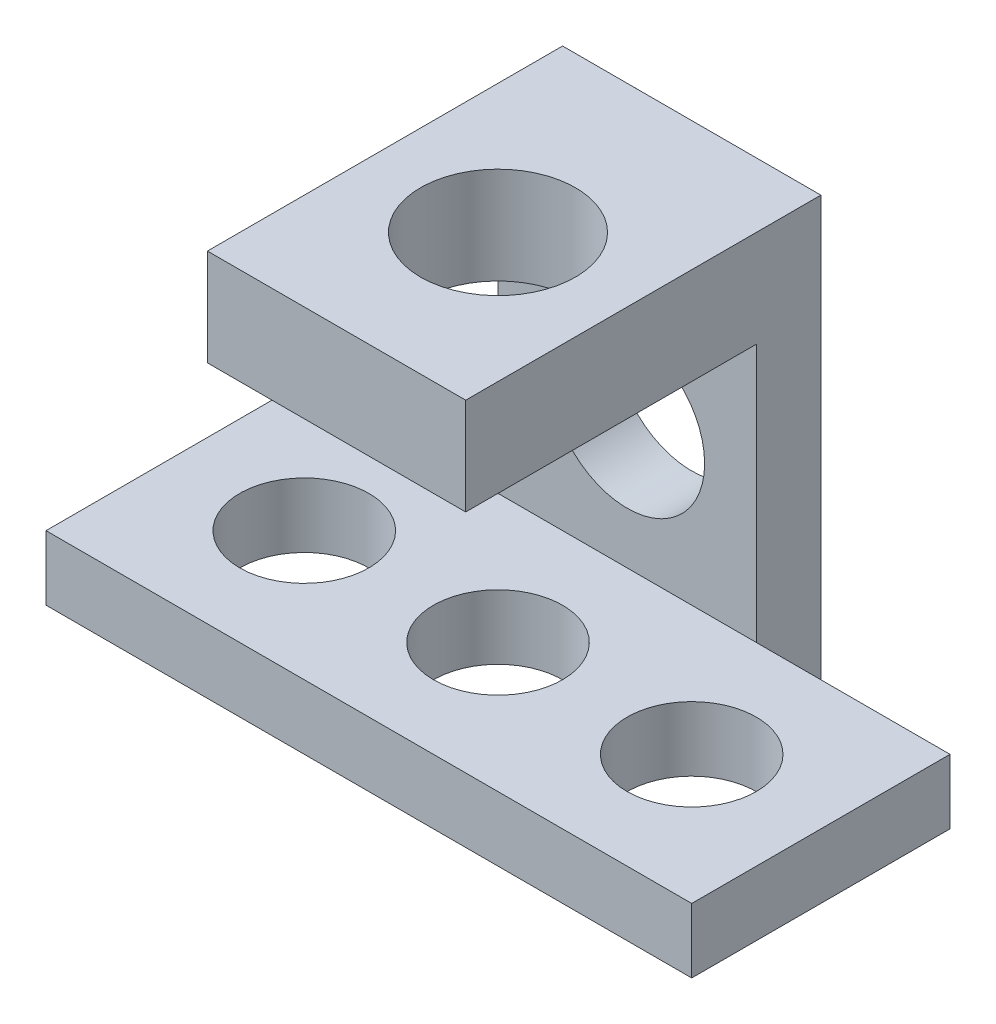
SolidWorks part; units mm, degrees
ref_plane "Front Plane" through (0, 0, 0) normal (0, 0, 1) x (1, 0, 0)
ref_plane "Top Plane" through (0, 0, 0) normal (0, 1, 0) x (1, 0, 0)
ref_plane "Right Plane" through (0, 0, 0) normal (1, 0, 0) x (0, 0, -1)
sketch "Sketch2" plane through (0, 0, 0) normal (0, 1, 0) x (1, 0, 0)
  line L0 (0, 0) -> (100, 0)
  line L1 (100, 0) -> (100, 40)
  line L2 (100, 40) -> (70, 40)
  line L3 (70, 40) -> (70, 50)
  line L4 (70, 50) -> (30, 50)
  line L5 (30, 50) -> (30, 40)
  line L6 (30, 40) -> (0, 40)
  line L7 (0, 40) -> (0, 0)
  dimension "D1" = 100
  dimension "D2" = 30
  dimension "D3" = 40
  dimension "D4" = 40
  dimension "D5" = 40
  dimension "D6" = 10
extrude "Boss-Extrude1" add sketch "Sketch2" along normal blind 10
sketch "Sketch3" plane through (0, 10, 0) normal (0, 1, 0) x (1, 0, 0)
  line L0 (100, 40) -> (70, 40) construction
  circle A0 centre (80, 20) radius 10
  circle A1 centre (50, 20) radius 10
  circle A2 centre (20, 20) radius 10
  dimension "D3" = 20
  dimension "D1" = 20
  dimension "D2" = 20
  dimension "D5" = 20
  dimension "D4" = 3
extrude "Cut-Extrude1" cut sketch "Sketch3" against normal blind 10
sketch "Sketch4" plane through (0, 10, 0) normal (0, 1, 0) x (1, 0, 0)
  line L0 (70, 40) -> (30, 40)
  line L1 (30, 40) -> (30, 50)
  line L2 (30, 50) -> (30, 40) construction
  line L3 (30, 50) -> (70, 50)
  line L4 (70, 50) -> (70, 40)
extrude "Boss-Extrude3" add sketch "Sketch4" along normal blind 55
sketch "Sketch6" plane through (0, 0, -40) normal (0, 0, 1) x (1, 0, 0)
  circle A0 centre (50, 30) radius 12
  dimension "D3" = 24
  dimension "D1" = 20
  dimension "D2" = 20
extrude "Cut-Extrude2" cut sketch "Sketch6" against normal blind 10
sketch "Sketch7" plane through (0, 0, -40) normal (0, 0, 1) x (1, 0, 0)
  line L0 (30, 50) -> (70, 50)
  line L1 (30, 65) -> (30, 10) construction
  line L2 (70, 65) -> (70, 10) construction
  line L3 (70, 50) -> (70, 65)
  line L4 (70, 65) -> (30, 65)
  line L5 (30, 65) -> (70, 65) construction
  line L6 (30, 65) -> (30, 50)
  dimension "D1" = 15
extrude "Boss-Extrude4" add sketch "Sketch7" along normal blind 45
sketch "Sketch8" plane through (0, 65, 0) normal (0, 1, 0) x (1, 0, 0)
  circle A0 centre (50, 20) radius 12
  dimension "D3" = 24
  dimension "D1" = 25
  dimension "D2" = 20
extrude "Cut-Extrude3" cut sketch "Sketch8" against normal blind 15
